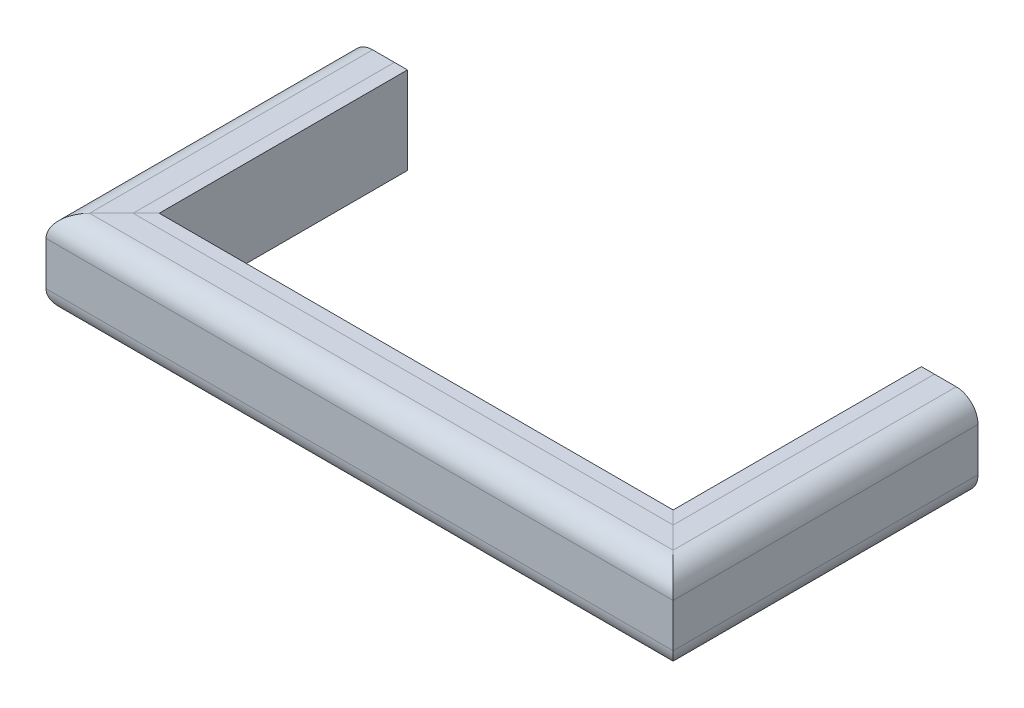
SolidWorks part; units mm, degrees
ref_plane "Front" through (0, 0, 0) normal (0, 0, 1) x (1, 0, 0)
ref_plane "Top" through (0, 0, 0) normal (0, 1, 0) x (1, 0, 0)
ref_plane "Right" through (0, 0, 0) normal (1, 0, 0) x (0, 0, -1)
sketch "Sketch1" plane through (0, 0, 0) normal (0, 0, 1) x (1, 0, 0)
  line L0 (-374.65, 0) -> (374.65, 0) construction
  line L1 (-393.7, 127) -> (-425.45, 127)
  line L2 (-374.65, 0) -> (-393.7, 0)
  line L3 (-374.65, 0) -> (-374.65, 127)
  line L4 (-374.65, 127) -> (-393.7, 127)
  line L5 (-393.7, 0) -> (-393.7, 127) construction
  line L6 (-457.2, 95.25) -> (-457.2, 31.75)
  line L7 (-425.45, 0) -> (-393.7, 0)
  circle A0 centre (-425.45, 95.25) radius 31.75 construction
  circle A1 centre (-425.45, 31.75) radius 31.75 construction
  arc A2 (-425.45, 127) -> (-457.2, 95.25) centre (-425.45, 95.25) ccw
  arc A3 (-457.2, 31.75) -> (-425.45, 0) centre (-425.45, 31.75) ccw
  dimension "D2" = 19.05
  dimension "D3" = 63.5
  dimension "D1" = 749.3
sketch "Sketch2" plane through (0, 0, 0) normal (0, 1, 0) x (1, 0, 0)
  line L0 (-374.65, 0) -> (-374.65, -361.95)
  line L1 (-374.65, 0) -> (374.65, 0) construction
  line L2 (-374.65, -361.95) -> (374.65, -361.95)
  line L3 (374.65, -361.95) -> (374.65, 0)
  dimension "D1" = 361.95
sweep "Sweep1" add profiles "Sketch1" path "Sketch2"
